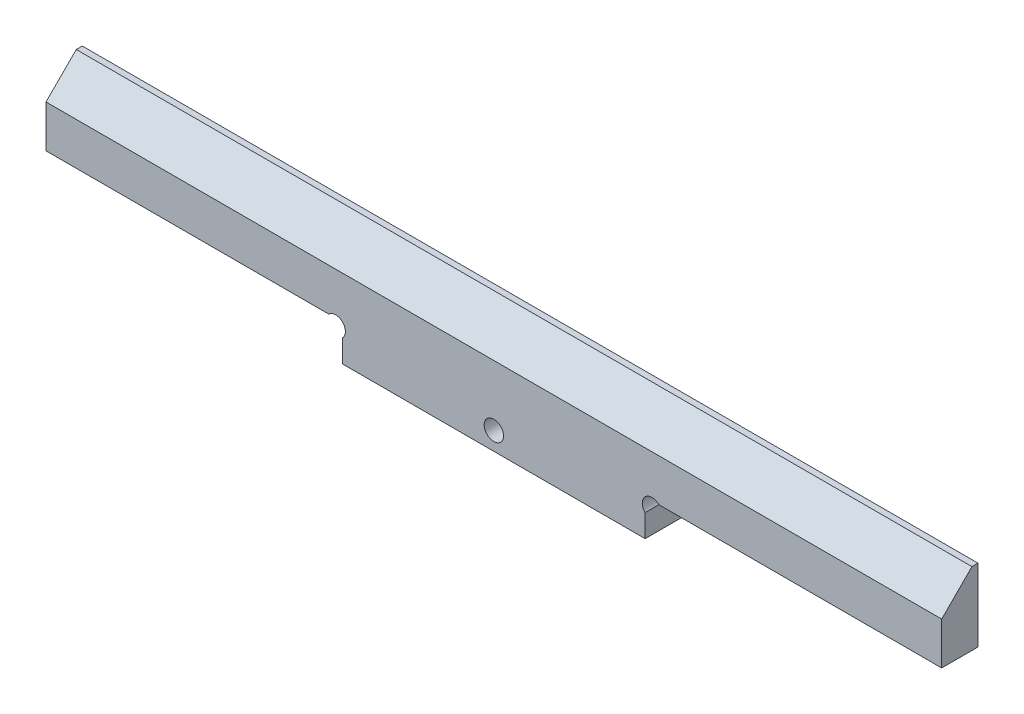
SolidWorks part; units mm, degrees
ref_plane "Plan de face" through (0, 0, 0) normal (0, 0, 1) x (1, 0, 0)
ref_plane "Plan de dessus" through (0, 0, 0) normal (0, 1, 0) x (1, 0, 0)
ref_plane "Plan de droite" through (0, 0, 0) normal (1, 0, 0) x (0, 0, -1)
sketch "Esquisse1" plane through (0, 0, 0) normal (0, 0, 1) x (1, 0, 0)
  line L0 (-13.6999, 0) -> (154.8584, 0) construction
  line L1 (0, -26.0659) -> (0, 30.2399) construction
  line L2 (148, -12.4019) -> (148, 30.2399) construction
  line L3 (-13.6999, 6) -> (154.8584, 6) construction
  line L4 (-13.6999, 18) -> (154.8584, 18) construction
  line L5 (74, 10.9417) -> (74, -26.0659) construction
  line L6 (49, 6) -> (36.1913, -6.8087) construction
  line L7 (86.9936, 3) -> (70.0603, 3) construction
  line L8 (49, -18.4186) -> (49, 10.9417) construction
  line L9 (49, 3.7373) -> (49, 0)
  line L10 (49, 0) -> (99, 0)
  line L11 (99, 0) -> (99, 3.7373)
  line L12 (46.7373, 6) -> (0, 6)
  line L13 (0, 6) -> (0, 18)
  line L14 (0, 18) -> (148, 18)
  line L15 (148, 18) -> (148, 6)
  line L16 (148, 6) -> (101.2627, 6)
  arc A0 (49, 3.7373) -> (46.7373, 6) centre (47.8686, 4.8686) ccw
  arc A1 (99, 3.7373) -> (101.2627, 6) centre (100.1314, 4.8686) cw
  circle A2 centre (74, 3) radius 1.6
  dimension "D1" = 148
  dimension "D2" = 6
  dimension "D3" = 12
  dimension "D4" = 74
  dimension "D5" = 25
  dimension "D6" = 3
  dimension "D7" = 45
extrude "Boss.-Extru.1" add sketch "Esquisse1" along normal blind 6
sketch "Esquisse2" plane through (0, 0, 0) normal (-1, 0, 0) x (0, 0, 1)
  line L0 (6.6111, 18) -> (-0.2869, 18) construction
  line L1 (0, 20.4451) -> (0, 12.5272) construction
  line L2 (0, 18) -> (0, 6) construction
  line L3 (6, 19.11) -> (6, 9.2636) construction
  line L4 (6, 18) -> (6, 6) construction
  line L5 (1, 19.11) -> (1, 12.5272) construction
  line L6 (1, 18) -> (7.0785, 11.9215) construction
  line L7 (1, 18) -> (6, 13)
  line L8 (6, 13) -> (6, 18)
  line L9 (6, 18) -> (1, 18)
  dimension "D1" = 1
  dimension "D2" = 45
extrude "Enlèv. mat.-Extru.1" cut sketch "Esquisse2" against normal through all
